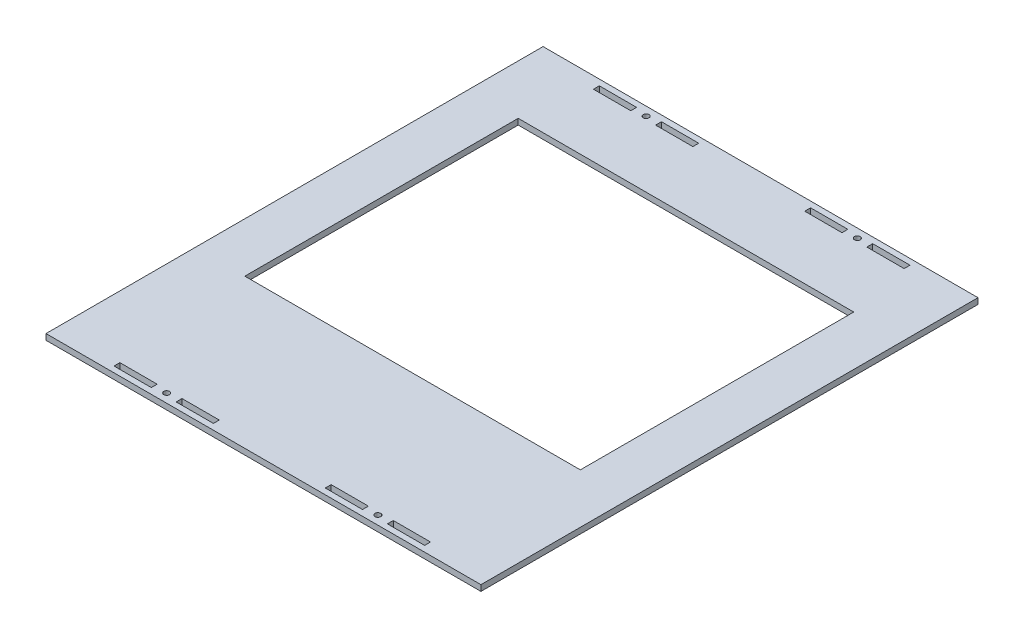
SolidWorks part; units mm, degrees
ref_plane "Front Plane" through (0, 0, 0) normal (0, 0, 1) x (1, 0, 0)
ref_plane "Top Plane" through (0, 0, 0) normal (0, 1, 0) x (1, 0, 0)
ref_plane "Right Plane" through (0, 0, 0) normal (1, 0, 0) x (0, 0, -1)
sketch "Sketch2" plane through (0, 0, 0) normal (0, 1, 0) x (1, 0, 0)
  line L1 (0, 0) -> (222.25, 0)
  line L2 (0, 0) -> (0, 254)
  line L3 (0, 254) -> (222.25, 254)
  line L4 (222.25, 0) -> (222.25, 254)
  dimension "D1" = 222.25
  dimension "D2" = 254
extrude "Boss-Extrude1" add sketch "Sketch2" along normal blind 3
sketch "Sketch5" plane through (0, 3, 0) normal (0, 1, 0) x (1, 0, 0)
  line L0 (222.25, 254) -> (0, 254) construction
  line L1 (31.75, 251) -> (50.8, 251)
  line L2 (31.75, 251) -> (31.75, 248)
  line L3 (31.75, 248) -> (50.8, 248)
  line L4 (50.8, 251) -> (50.8, 248)
  line L5 (50.8, 249.5) -> (63.5, 249.5) construction
  line L6 (57.15, 249.5) -> (57.15, 254) construction
  line L7 (63.5, 251) -> (82.5512, 251)
  line L8 (63.5, 251) -> (63.5, 248)
  line L9 (63.5, 248) -> (82.5512, 248)
  line L10 (82.5512, 251) -> (82.5512, 248)
  line L11 (0, 254) -> (0, 0) construction
  line L12 (111.125, 254) -> (111.125, 0) construction
  line L13 (0, 0) -> (222.25, 0) construction
  line L14 (0, 127) -> (222.25, 127) construction
  line L15 (222.25, 0) -> (222.25, 254) construction
  line L16 (158.75, 251) -> (158.75, 248)
  line L17 (171.45, 251) -> (171.45, 248)
  line L18 (158.75, 248) -> (139.6988, 248)
  line L19 (139.6988, 251) -> (139.6988, 248)
  line L20 (158.75, 251) -> (139.6988, 251)
  line L21 (190.5, 248) -> (171.45, 248)
  line L22 (190.5, 251) -> (190.5, 248)
  line L23 (190.5, 251) -> (171.45, 251)
  line L24 (31.75, 3) -> (31.75, 6)
  line L25 (31.75, 6) -> (50.8, 6)
  line L26 (31.75, 3) -> (50.8, 3)
  line L27 (50.8, 3) -> (50.8, 6)
  line L28 (63.5, 3) -> (63.5, 6)
  line L29 (82.5512, 3) -> (82.5512, 6)
  line L30 (63.5, 6) -> (82.5512, 6)
  line L31 (63.5, 3) -> (82.5512, 3)
  line L32 (190.5, 3) -> (171.45, 3)
  line L33 (190.5, 3) -> (190.5, 6)
  line L34 (190.5, 6) -> (171.45, 6)
  line L35 (158.75, 3) -> (139.6988, 3)
  line L36 (139.6988, 3) -> (139.6988, 6)
  line L37 (158.75, 6) -> (139.6988, 6)
  line L38 (171.45, 3) -> (171.45, 6)
  line L39 (158.75, 3) -> (158.75, 6)
  dimension "D1" = 3
  dimension "D2" = 3
  dimension "D3" = 19.05
  dimension "D4" = 3
  dimension "D5" = 19.0512
  dimension "D6" = 12.7
  dimension "D7" = 57.15
extrude "Cut-Extrude1" cut sketch "Sketch5" against normal through all
hole_wizard "#4 Clearance Hole2" positions "Sketch7" profile "Sketch6" hole size "#4" standard "ANSI Inch" end condition through all
sketch "Sketch7" plane through (0, 3, 0) normal (0, 1, 0) x (1, 0, 0)
  line L0 (158.75, 249.5) -> (171.45, 249.5) construction
  line L1 (158.75, 251) -> (158.75, 248) construction
  line L2 (171.45, 251) -> (171.45, 248) construction
  line L4 (158.75, 4.5) -> (171.45, 4.5) construction
  line L5 (158.75, 3) -> (158.75, 6) construction
  line L6 (171.45, 3) -> (171.45, 6) construction
  line L8 (50.8, 4.5) -> (63.5, 4.5) construction
  line L9 (50.8, 3) -> (50.8, 6) construction
  line L10 (63.5, 3) -> (63.5, 6) construction
  point P0 (57.15, 249.5)
  point P3 (165.1, 249.5)
  point P5 (165.1, 4.5)
  point P7 (57.15, 4.5)
  point P18 (165.1, 249.5)
  point P26 (165.1, 4.5)
  point P35 (57.15, 4.5)
sketch "Sketch6" plane through (57.15, 3, -249.5) normal (1, 0, 0) x (0, 0, 1)
  line L0 (0, 0) -> (0, 3)
  line L1 (0, 3) -> (1.4732, 3)
  line L2 (1.4732, 3) -> (1.4732, 0)
  line L5 (1.4732, 0) -> (0, 0)
  line L11 (0, -6.35) -> (0, 107.95) construction
  dimension "Thru Hole Dia." = 2.9464
  dimension "Thru Hole Depth" = 3
sketch "Sketch8" plane through (0, 3, 0) normal (0, 1, 0) x (1, 0, 0)
  line L0 (0, 0) -> (222.25, 0) construction
  line L1 (25.4, 215.9) -> (196.85, 215.9)
  line L2 (25.4, 215.9) -> (25.4, 76.2)
  line L3 (25.4, 76.2) -> (196.85, 76.2)
  line L4 (196.85, 215.9) -> (196.85, 76.2)
  line L5 (222.25, 254) -> (0, 254) construction
  line L6 (0, 254) -> (0, 0) construction
  line L7 (222.25, 0) -> (222.25, 254) construction
  dimension "D1" = 76.2
  dimension "D2" = 38.1
  dimension "D3" = 25.4
  dimension "D4" = 25.4
extrude "Cut-Extrude2" cut sketch "Sketch8" against normal through all
